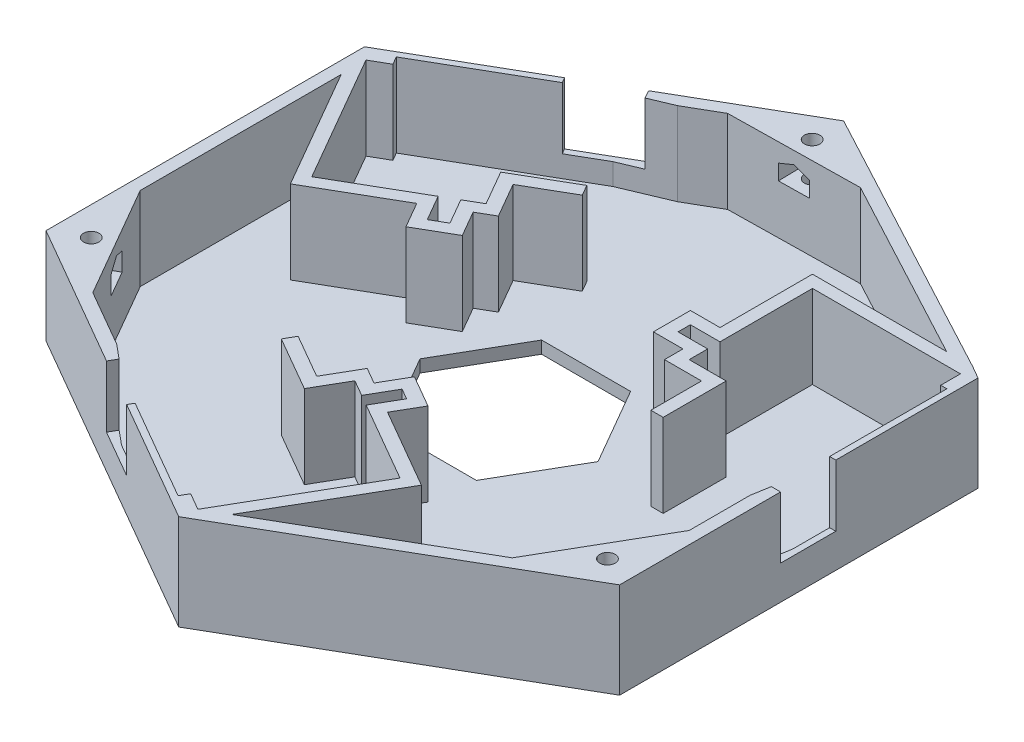
SolidWorks part; units mm, degrees
ref_plane "Front Plane" through (0, 0, 0) normal (0, 0, 1) x (1, 0, 0)
ref_plane "Top Plane" through (0, 0, 0) normal (0, 1, 0) x (1, 0, 0)
ref_plane "Right Plane" through (0, 0, 0) normal (1, 0, 0) x (0, 0, -1)
sketch "Sketch1" plane through (0, 0, 0) normal (0, 1, 0) x (1, 0, 0)
  line L1 (127, 0) -> (-63.5, 109.9852)
  line L2 (-63.5, 109.9852) -> (-63.5, -109.9852)
  line L3 (-63.5, -109.9852) -> (127, 0)
  circle A0 centre (0, 0) radius 63.5 construction
  dimension "D1" = 127
extrude "Boss-Extrude1" add sketch "Sketch1" along normal blind 15.5
sketch "Sketch2" plane through (0, 15.5, 0) normal (0, 1, 0) x (1, 0, 0)
  line L0 (-63.5, -109.9852) -> (16.5, -63.7972)
  line L1 (-63.5, -109.9852) -> (127, 0) construction
  line L2 (-63.5, 109.9852) -> (-63.5, -109.9852) construction
  line L3 (16.5, -63.7972) -> (-63.5, -17.6092)
  line L4 (-63.5, -17.6092) -> (-63.5, -109.9852)
  line L5 (-63.5, 109.9852) -> (16.5, 63.7972)
  line L6 (127, 0) -> (-63.5, 109.9852) construction
  line L7 (16.5, 63.7972) -> (-63.5, 17.6092)
  line L8 (-63.5, 17.6092) -> (-63.5, 109.9852)
  line L9 (127, 0) -> (47, 46.188)
  line L10 (47, 46.188) -> (47, -46.188)
  line L11 (47, -46.188) -> (127, 0)
  dimension "D1" = 80
  dimension "D2" = 110.5
extrude "Cut-Extrude1" cut sketch "Sketch2" against normal blind 24
sketch "Sketch3" plane through (0, 15.5, 0) normal (0, 1, 0) x (1, 0, 0)
  line L0 (47, 0) -> (-63.5, 0) construction
  line L1 (47, 46.188) -> (47, -46.188) construction
  line L2 (-63.5, 17.6092) -> (-63.5, -17.6092) construction
  line L3 (-23.5, 40.7032) -> (31.75, -54.9926) construction
  line L4 (-63.5, 17.6092) -> (16.5, 63.7972) construction
  line L5 (16.5, -63.7972) -> (47, -46.188) construction
  line L6 (-23.5, -40.7032) -> (31.75, 54.9926) construction
  line L7 (16.5, -63.7972) -> (-63.5, -17.6092) construction
  line L8 (47, 46.188) -> (16.5, 63.7972) construction
  line L14 (21, 28.2173) -> (21, 13.2173)
  line L15 (21, 13.2173) -> (16.2, 13.2173)
  line L25 (16.2, 13.2173) -> (16.2, 11.2173)
  line L26 (16.2, 11.2173) -> (21, 11.2173)
  line L27 (21, 11.2173) -> (21, 8.2173)
  line L28 (21, 8.2173) -> (27, 8.2173)
  line L38 (45, 28.2173) -> (21, 28.2173)
  line L41 (46, 21.2173) -> (46, 25.0173)
  line L42 (46, 25.0173) -> (45, 25.0173)
  line L43 (45, 25.0173) -> (45, 28.2173)
  line L84 (27, 8.2173) -> (27, 0)
  line L85 (27, 0) -> (45, 0)
  line L91 (14.1869, -31.8622) -> (1.1965, -24.3622)
  line L92 (1.1965, -24.3622) -> (3.5965, -20.2052)
  line L93 (3.5965, -20.2052) -> (1.8644, -19.2052)
  line L94 (1.8644, -19.2052) -> (-0.5356, -23.3622)
  line L95 (-0.5356, -23.3622) -> (-3.1336, -21.8622)
  line L96 (-3.1336, -21.8622) -> (-6.1336, -27.0583)
  line L97 (2.1869, -52.6468) -> (14.1869, -31.8622)
  line L99 (-4.6253, -50.4458) -> (-1.3344, -52.3458)
  line L100 (-1.3344, -52.3458) -> (-0.5844, -51.0468)
  line L101 (-0.5844, -51.0468) -> (2.1869, -52.6468)
  line L102 (-6.1336, -27.0583) -> (-13.25, -22.9497)
  line L103 (-13.25, -22.9497) -> (-22.25, -38.5381)
  line L105 (-35.285, 3.2995) -> (-22.2947, 10.7995)
  line L106 (-22.2947, 10.7995) -> (-19.8947, 6.6426)
  line L107 (-19.8947, 6.6426) -> (-17.5644, 7.988)
  line L108 (-17.5644, 7.988) -> (-19.9644, 12.1449)
  line L109 (-19.9644, 12.1449) -> (-17.3664, 13.6449)
  line L110 (-17.3664, 13.6449) -> (-20.6164, 19.2741)
  line L111 (-47.285, 24.0841) -> (-35.285, 3.2995)
  line L113 (-41.3747, 29.2285) -> (-45.2638, 26.9832)
  line L114 (-45.2638, 26.9832) -> (-44.5138, 25.6841)
  line L115 (-44.5138, 25.6841) -> (-47.285, 24.0841)
  line L116 (-20.6164, 19.2741) -> (-13.5, 23.3827)
  line L117 (-13.5, 23.3827) -> (-22.5, 38.9711)
  line L119 (-22.25, -38.5381) -> (-23, -39.8372)
  line L120 (-23, -39.8372) -> (-4.6253, -50.4458)
  line L121 (-41.3747, 29.2285) -> (-23, 39.8372)
  line L122 (-23, 39.8372) -> (-22.5, 38.9711)
  line L123 (45, 0) -> (46, 0)
  line L124 (46, 0) -> (46, 21.2173)
  dimension "D1" = 8.2173
  dimension "D2" = 3
  dimension "D3" = 4.8
  dimension "D4" = 6
  dimension "D5" = 2
  dimension "D6" = 15
  dimension "D7" = 24
  dimension "D8" = 1
  dimension "D9" = 3.8
  dimension "D12" = 1.5
  dimension "D13" = 1
  dimension "D14" = 24
  dimension "D15" = 18
  dimension "D16" = 18
  dimension "D17" = 6
  dimension "D18" = 4.8
  dimension "D19" = 1
  dimension "D21" = 8.2173
  dimension "D22" = 3.2
  dimension "D23" = 15
  dimension "D24" = 4.8
  dimension "D26" = 3
extrude "Cut-Extrude2" cut sketch "Sketch3" against normal blind 13.5
sketch "Sketch4" plane through (0, 15.5, 0) normal (0, 1, 0) x (1, 0, 0)
  line L0 (3.6689, -54.0798) -> (16.5, -61.4878)
  line L4 (25, -2) -> (25, 6.2173)
  line L5 (25, 6.2173) -> (19, 6.2173)
  line L6 (19, 6.2173) -> (19, 9.2173)
  line L7 (19, 9.2173) -> (14.2, 9.2173)
  line L8 (14.2, 9.2173) -> (14.2, 15.2173)
  line L9 (14.2, 15.2173) -> (19, 15.2173)
  line L10 (19, 15.2173) -> (19, 30.2173)
  line L11 (19, 30.2173) -> (45, 30.2173)
  line L12 (45, 30.2173) -> (45, 45.0333)
  line L13 (45, 45.0333) -> (26.5, 55.7143)
  line L14 (26.5, 55.7143) -> (6.5, 55.7143)
  line L17 (-10.7679, 22.6506) -> (-17.8843, 18.542)
  line L18 (-17.8843, 18.542) -> (-14.6343, 12.9128)
  line L19 (-14.6343, 12.9128) -> (-17.2324, 11.4128)
  line L20 (-17.2324, 11.4128) -> (-14.8324, 7.2559)
  line L21 (-14.8324, 7.2559) -> (-20.6267, 3.9106)
  line L22 (-20.6267, 3.9106) -> (-23.0267, 8.0675)
  line L23 (-23.0267, 8.0675) -> (-36.0171, 0.5675)
  line L24 (-36.0171, 0.5675) -> (-49.2671, 23.5172)
  line L25 (-49.2671, 23.5172) -> (-61.5, 16.4545)
  line L26 (-61.5, 16.4545) -> (-61.5, -4.9075)
  line L27 (-61.5, -4.9075) -> (-51.5, -22.228)
  line L30 (-13.9821, -20.2176) -> (-6.8657, -24.3263)
  line L31 (-6.8657, -24.3263) -> (-3.8657, -19.1301)
  line L32 (-3.8657, -19.1301) -> (-1.2676, -20.6301)
  line L33 (-1.2676, -20.6301) -> (1.1324, -16.4732)
  line L34 (1.1324, -16.4732) -> (6.3285, -19.4732)
  line L35 (6.3285, -19.4732) -> (3.9285, -23.6301)
  line L36 (3.9285, -23.6301) -> (16.9189, -31.1301)
  line L37 (16.9189, -31.1301) -> (3.6689, -54.0798)
  line L38 (16.5, -61.4878) -> (35, -50.8068)
  line L39 (35, -50.8068) -> (45, -33.4863)
  line L41 (-63.5, 17.6092) -> (-63.5, -17.6092) construction
  line L42 (16.5, -63.7972) -> (-63.5, -17.6092) construction
  line L43 (-17.5644, 7.988) -> (-19.9644, 12.1449) construction
  line L44 (-6.1336, -27.0583) -> (-13.25, -22.9497) construction
  line L45 (-3.1336, -21.8622) -> (-6.1336, -27.0583) construction
  line L46 (16.5, -63.7972) -> (47, -46.188) construction
  line L47 (2.1869, -52.6468) -> (14.1869, -31.8622) construction
  line L48 (14.1869, -31.8622) -> (1.1965, -24.3622) construction
  line L49 (1.8644, -19.2052) -> (-0.5356, -23.3622) construction
  line L50 (1.1965, -24.3622) -> (3.5965, -20.2052) construction
  line L51 (47, 46.188) -> (47, -46.188) construction
  line L52 (-47.285, 24.0841) -> (-35.285, 3.2995) construction
  line L53 (-63.5, 17.6092) -> (16.5, 63.7972) construction
  line L54 (47, 46.188) -> (16.5, 63.7972) construction
  line L55 (-35.285, 3.2995) -> (-22.2947, 10.7995) construction
  line L56 (-22.2947, 10.7995) -> (-19.8947, 6.6426) construction
  line L57 (-19.8947, 6.6426) -> (-17.5644, 7.988) construction
  line L58 (-19.9644, 12.1449) -> (-17.3664, 13.6449) construction
  line L59 (-17.3664, 13.6449) -> (-20.6164, 19.2741) construction
  line L60 (-20.6164, 19.2741) -> (-13.5, 23.3827) construction
  line L62 (14.1869, -31.8622) -> (1.1965, -24.3622) construction
  line L63 (3.5965, -20.2052) -> (1.8644, -19.2052) construction
  line L64 (-0.5356, -23.3622) -> (-3.1336, -21.8622) construction
  line L65 (-6.1336, -27.0583) -> (-13.25, -22.9497) construction
  line L67 (45, 28.2173) -> (21, 28.2173) construction
  line L69 (16.2, 11.2173) -> (21, 11.2173) construction
  line L70 (21, 13.2173) -> (16.2, 13.2173) construction
  line L71 (16.2, 13.2173) -> (16.2, 11.2173) construction
  line L72 (21, 28.2173) -> (21, 13.2173) construction
  line L73 (21, 8.2173) -> (27, 8.2173) construction
  line L74 (21, 11.2173) -> (21, 8.2173) construction
  line L75 (27, 8.2173) -> (27, 0) construction
  line L76 (-13.9821, -20.2176) -> (-23.7321, -37.1051)
  line L77 (-51.5, -22.228) -> (-27.6235, -36.0131)
  line L78 (-27.6235, -36.0131) -> (-23, -39.8372)
  line L79 (-23, -39.8372) -> (-22, -38.1051)
  line L80 (-13.25, -22.9497) -> (-23, -39.8372) construction
  line L81 (-22, -38.1051) -> (-23.7321, -37.1051)
  line L82 (6.5, 55.7143) -> (-15.6261, 42.9398)
  line L83 (-15.6261, 42.9398) -> (-23, 39.8372)
  line L84 (-23, 39.8372) -> (-22, 38.1051)
  line L85 (-13.5, 23.3827) -> (-23, 39.8372) construction
  line L86 (-22, 38.1051) -> (-20.2679, 39.1051)
  line L87 (-20.2679, 39.1051) -> (-10.7679, 22.6506)
  line L88 (45, -33.4863) -> (45, -5.9161)
  line L89 (45, -5.9161) -> (46, 0)
  line L90 (46, 0) -> (44, 0)
  line L91 (27, 0) -> (46, 0) construction
  line L92 (44, 0) -> (44, -2)
  line L93 (44, -2) -> (25, -2)
  point P75 (-15.9333, 12.1628)
  point P88 (-1.8346, -22.6122)
  point P89 (-4.6336, -24.4602)
  point P98 (31.75, -54.9926)
  dimension "D2" = 2
  dimension "D4" = 2
  dimension "D5" = 2
  dimension "D6" = 2
  dimension "D7" = 2
  dimension "D8" = 2
  dimension "D9" = 2
  dimension "D10" = 2
  dimension "D11" = 2
  dimension "D12" = 2
  dimension "D13" = 2
  dimension "D14" = 2
  dimension "D15" = 2
  dimension "D16" = 2
  dimension "D17" = 2
  dimension "D18" = 2
  dimension "D19" = 2
  dimension "D20" = 2
  dimension "D21" = 2
  dimension "D22" = 2
  dimension "D23" = 2
  dimension "D24" = 2
  dimension "D25" = 2
  dimension "D26" = 6
  dimension "D27" = 2
  dimension "D28" = 2
  dimension "D29" = 2
  dimension "D30" = 2
  dimension "D31" = 2
  dimension "D32" = 2
  dimension "D33" = 2
  dimension "D34" = 2
  dimension "D35" = 2
  dimension "D36" = 20
  dimension "D37" = 20
  dimension "D38" = 20
  dimension "D39" = 2
  dimension "D40" = 6
  dimension "D41" = 2
  dimension "D42" = 8
  dimension "D43" = 2
  dimension "D44" = 2
  dimension "D45" = 2
  dimension "D46" = 2
  dimension "D47" = 2
extrude "Cut-Extrude3" cut sketch "Sketch4" against normal blind 13.5
sketch "Sketch5" plane through (0, 2, 0) normal (0, 1, 0) x (1, 0, 0)
  line L1 (14.4338, 0) -> (7.2169, 12.5)
  line L2 (7.2169, 12.5) -> (-7.2169, 12.5)
  line L3 (-7.2169, 12.5) -> (-14.4338, 0)
  line L4 (-14.4338, 0) -> (-7.2169, -12.5)
  line L5 (-7.2169, -12.5) -> (7.2169, -12.5)
  line L6 (7.2169, -12.5) -> (14.4338, 0)
  circle A0 centre (0, 0) radius 12.5 construction
  dimension "D1" = 25
extrude "Cut-Extrude4" cut sketch "Sketch5" against normal blind 13.5
sketch "Sketch6" plane through (0, 15.5, 0) normal (0, 1, 0) x (1, 0, 0)
  line L6 (41.75, -43.1569) -> (43.5, -44.1673) construction
  line L7 (-58.25, -14.5781) -> (-60, -15.5885) construction
  line L8 (16.5, 57.735) -> (16.5, 59.7558) construction
  circle A3 centre (-59.125, -15.0833) radius 1.15
  circle A4 centre (16.5, 58.7454) radius 1.15
  circle A5 centre (42.625, -43.6621) radius 1.15
  dimension "D1" = 2.3
  dimension "D2" = 2.3
  dimension "D3" = 2.3
extrude "Cut-Extrude5" cut sketch "Sketch6" against normal blind 10.5
sketch "Sketch8" plane through (-48.25, 0, 27.8572) normal (0.866, 0, -0.5) x (-0.5, 0, -0.866)
  line L0 (16.5, 15.5) -> (16.5, 5.1)
  line L3 (26.5, 15.5) -> (6.5, 15.5) construction
  line L9 (14, 6.1) -> (19, 6.1)
  line L10 (14, 6.1) -> (14, 4.1)
  line L11 (14, 4.1) -> (19, 4.1)
  line L12 (19, 6.1) -> (19, 4.1)
  line L13 (14, 6.1) -> (19, 4.1) construction
  line L14 (14, 4.1) -> (19, 6.1) construction
  point P6 (16.5, 9.7316)
  dimension "D1" = 2
  dimension "D2" = 5
  dimension "D3" = 10.4
extrude "Cut-Extrude7" cut sketch "Sketch8" against normal blind 5.5 contours L9 L12 L11 L10
sketch "Sketch9" plane through (48.25, 0, 27.8572) normal (-0.866, 0, -0.5) x (-0.5, 0, 0.866)
  line L0 (16.5, 15.5) -> (16.5, 5.1) construction
  line L1 (26.5, 15.5) -> (6.5, 15.5) construction
  line L3 (14, 6.1) -> (19, 6.1)
  line L4 (14, 6.1) -> (14, 4.1)
  line L5 (14, 4.1) -> (19, 4.1)
  line L6 (19, 6.1) -> (19, 4.1)
  line L7 (14, 6.1) -> (19, 4.1) construction
  line L8 (14, 4.1) -> (19, 6.1) construction
  dimension "D1" = 2
  dimension "D2" = 5
extrude "Cut-Extrude8" cut sketch "Sketch9" against normal blind 5.5
sketch "Sketch10" plane through (0, 0, -55.7143) normal (0, 0, 1) x (1, 0, 0)
  line L0 (16.5, 15.5) -> (16.5, 5.1) construction
  line L1 (26.5, 15.5) -> (6.5, 15.5) construction
  line L3 (14, 6.1) -> (19, 6.1)
  line L4 (14, 6.1) -> (14, 4.1)
  line L5 (14, 4.1) -> (19, 4.1)
  line L6 (19, 6.1) -> (19, 4.1)
  line L7 (14, 6.1) -> (19, 4.1) construction
  line L8 (14, 4.1) -> (19, 6.1) construction
  dimension "D1" = 2
  dimension "D2" = 5
extrude "Cut-Extrude9" cut sketch "Sketch10" against normal blind 5.5
sketch "Sketch12" plane through (0, 15.5, 0) normal (0, 1, 0) x (1, 0, 0)
  line L0 (-49.2671, 23.5172) -> (-49.2671, -25.8266)
  line L1 (16.5, -63.7972) -> (-63.5, -17.6092) construction
  line L2 (-49.2671, -25.8266) -> (-63.5, -17.6092)
  line L3 (-63.5, -17.6092) -> (-63.5, 17.6092)
  line L4 (-63.5, 17.6092) -> (-49.2671, 25.8266)
  line L5 (-63.5, 17.6092) -> (16.5, 63.7972) construction
  line L6 (-49.2671, 25.8266) -> (-49.2671, 23.5172)
  line L7 (3.6689, -54.0798) -> (47, -29.0626)
  line L8 (47, 46.188) -> (47, -46.188) construction
  line L9 (47, -29.0626) -> (47, -46.188)
  line L10 (47, -46.188) -> (16.5, -63.7972)
  line L11 (16.5, -63.7972) -> (1.6689, -55.2345)
  line L12 (3.6689, -54.0798) -> (1.6689, -55.2345)
  line L13 (45, 30.2173) -> (0, 54.2709)
  line L14 (0, 54.2709) -> (16.5, 63.7972)
  line L15 (16.5, 63.7972) -> (47, 46.188)
  line L16 (47, 46.188) -> (16.5, 63.7972) construction
  line L17 (45, 30.2173) -> (47, 29.0626)
  line L18 (47, 29.0626) -> (47, 46.188)
extrude "Cut-Extrude10" cut sketch "Sketch12" against normal blind 20
sketch "Sketch13" plane through (0, 2, 0) normal (0, 1, 0) x (1, 0, 0)
  line L0 (-49.2671, -23.5172) -> (-49.2671, 23.5172)
  line L1 (-36.0171, 0.5675) -> (-49.2671, 23.5172) construction
  line L2 (-36.0171, 0.5675) -> (-49.2671, 23.5172) construction
  line L3 (-49.2671, 23.5172) -> (-47.2671, 20.0531)
  line L4 (-47.2671, 20.0531) -> (-47.2671, -24.6719)
  line L5 (-49.2671, -23.5172) -> (-27.6235, -36.0131) construction
  line L6 (-47.2671, -24.6719) -> (-49.2671, -23.5172)
  line L7 (45, -30.2173) -> (3.6689, -54.0798)
  line L8 (3.6689, -54.0798) -> (5.6689, -50.6157)
  line L9 (16.9189, -31.1301) -> (3.6689, -54.0798) construction
  line L10 (5.6689, -50.6157) -> (45, -27.9079)
  line L11 (45, -30.2173) -> (45, -5.9161) construction
  line L12 (45, -27.9079) -> (45, -30.2173)
  line L13 (45, 30.2173) -> (2.077, 53.1607)
  line L14 (0.0374, 51.9831) -> (40.7574, 30.2173)
  line L15 (2.077, 53.1607) -> (0.0374, 51.9831)
  line L16 (2.077, 53.1607) -> (-15.6261, 42.9398) construction
  line L17 (19, 30.2173) -> (45, 30.2173) construction
  line L18 (40.7574, 30.2173) -> (45, 30.2173)
  dimension "D1" = 2
  dimension "D2" = 2
  dimension "D3" = 2
extrude "Boss-Extrude2" add sketch "Sketch13" along normal blind 13.5
sketch "Sketch14" plane through (0, 2, 0) normal (0, 1, 0) x (1, 0, 0)
  line L0 (-47.2671, -24.6719) -> (-36.7671, -30.734)
  line L1 (-47.2671, -24.6719) -> (-27.6235, -36.0131) construction
  line L2 (-36.7671, -30.734) -> (-47.2671, -12.5475)
  line L3 (-47.2671, -24.6719) -> (-47.2671, 20.0531) construction
  line L4 (-47.2671, -12.5475) -> (-47.2671, -24.6719)
  line L5 (0.0374, 51.9831) -> (-10.4626, 45.921)
  line L6 (0.0374, 51.9831) -> (-15.6261, 42.9398) construction
  line L7 (-10.4626, 45.921) -> (10.7301, 46.2676)
  line L8 (0.0374, 51.9831) -> (40.7574, 30.2173) construction
  line L9 (10.7301, 46.2676) -> (0.0374, 51.9831)
  line L10 (45, -27.9079) -> (45, -15.7835)
  line L11 (45, -27.9079) -> (45, -5.9161) construction
  line L12 (45, -15.7835) -> (34.5, -33.97)
  line L13 (45, -27.9079) -> (5.6689, -50.6157) construction
  line L14 (34.5, -33.97) -> (45, -27.9079)
  dimension "D1" = 21
  dimension "D2" = 6.0622
  dimension "D3" = 21.1927
  dimension "D4" = 21
extrude "Boss-Extrude3" add sketch "Sketch14" along normal blind 13.5
sketch "Sketch15" plane through (0, 15.5, 0) normal (0, 1, 0) x (1, 0, 0)
  line L0 (-44.6152, -23.1408) -> (-42.0171, -21.6408) construction
  line L3 (0.0669, 49.0943) -> (0.1338, 46.0943) construction
  line L5 (42.3481, -26.3768) -> (39.75, -24.8768) construction
  line L7 (-36.7671, -30.734) -> (-47.2671, -12.5475) construction
  line L8 (-10.4626, 45.921) -> (10.7301, 46.2676) construction
  line L9 (45, -15.7835) -> (34.5, -33.97) construction
  circle A0 centre (-44.6152, -23.1408) radius 1.25
  circle A1 centre (42.3481, -26.3768) radius 1.25
  circle A2 centre (0.0669, 49.0943) radius 1.25
  dimension "D1" = 2.5
  dimension "D2" = 3
  dimension "D3" = 3
  dimension "D4" = 3
extrude "Cut-Extrude11" cut sketch "Sketch15" against normal blind 8.5
sketch "Sketch16" plane through (-0.7538, 0, -46.0798) normal (0.0164, 0, 0.9999) x (0.9999, 0, -0.0164)
  line L0 (0.8877, 15.5) -> (0.8877, 7) construction
  line L1 (0.8877, 12.5) -> (0.8877, 13.5) construction
  line L2 (-1.6123, 12.5) -> (0.8877, 13.5)
  line L3 (-9.7101, 15.5) -> (11.4854, 15.5) construction
  line L4 (0.8877, 13.5) -> (3.3877, 12.5)
  line L6 (-1.6123, 12.5) -> (-1.6123, 10)
  line L7 (-1.6123, 10) -> (3.3877, 10)
  line L8 (3.3877, 12.5) -> (3.3877, 10)
  line L9 (-1.6123, 12.5) -> (3.3877, 10) construction
  line L10 (-1.6123, 10) -> (3.3877, 12.5) construction
  point P4 (0.8877, 11.25)
  dimension "D1" = 2.5
  dimension "D2" = 5
sketch "Sketch17" plane through (-40.8835, 0, 23.6041) normal (0.866, 0, -0.5) x (-0.5, 0, -0.866)
  line L0 (2.2671, 15.5) -> (2.2671, 7) construction
  line L1 (-8.2329, 15.5) -> (12.7671, 15.5) construction
  line L2 (2.2671, 12.5) -> (2.2671, 13.5) construction
  line L4 (-0.2329, 12.5) -> (-0.2329, 9.5)
  line L5 (-0.2329, 9.5) -> (4.7671, 9.5)
  line L6 (4.7671, 12.5) -> (4.7671, 9.5)
  line L7 (-0.2329, 12.5) -> (4.7671, 9.5) construction
  line L8 (-0.2329, 9.5) -> (4.7671, 12.5) construction
  line L9 (-0.2329, 12.5) -> (2.2671, 13.5)
  line L10 (2.2671, 13.5) -> (4.7671, 12.5)
  point P4 (2.2671, 11)
  dimension "D1" = 5
  dimension "D2" = 3
sketch "Sketch18" plane through (40.5845, 0, 23.4314) normal (-0.866, 0, -0.5) x (-0.5, 0, 0.866)
  line L0 (1.6689, 15.5) -> (1.6689, 7) construction
  line L1 (-8.8311, 15.5) -> (12.1689, 15.5) construction
  line L2 (1.6689, 12.5) -> (1.6689, 13.5) construction
  line L4 (-0.8311, 12.5) -> (-0.8311, 9.5)
  line L5 (-0.8311, 9.5) -> (4.1689, 9.5)
  line L6 (4.1689, 12.5) -> (4.1689, 9.5)
  line L7 (-0.8311, 12.5) -> (4.1689, 9.5) construction
  line L8 (-0.8311, 9.5) -> (4.1689, 12.5) construction
  line L9 (-0.8311, 12.5) -> (1.6689, 13.5)
  line L10 (1.6689, 13.5) -> (4.1689, 12.5)
  point P4 (1.6689, 11)
  dimension "D1" = 5
  dimension "D2" = 3
sketch "Sketch19" plane through (0, 15.5, 0) normal (0, 1, 0) x (1, 0, 0)
  line L0 (-13.25, -22.9497) -> (-22, -38.1051)
  line L1 (-22, -38.1051) -> (-23.7321, -37.1051)
  line L2 (-23.7321, -37.1051) -> (-14.9821, -21.9497)
  line L3 (-23.7321, -37.1051) -> (-13.9821, -20.2176) construction
  line L4 (-14.9821, -21.9497) -> (-13.25, -22.9497)
  line L5 (-13.5, 23.3827) -> (-22, 38.1051)
  line L6 (-22, 38.1051) -> (-20.2679, 39.1051)
  line L7 (-20.2679, 39.1051) -> (-11.7679, 24.3827)
  line L8 (-20.2679, 39.1051) -> (-10.7679, 22.6506) construction
  line L9 (-11.7679, 24.3827) -> (-13.5, 23.3827)
  line L11 (27, 0) -> (44, 0)
  line L12 (27, 0) -> (27, -2)
  line L13 (27, -2) -> (44, -2)
  line L14 (44, 0) -> (44, -2)
extrude "Cut-Extrude15" cut sketch "Sketch19" against normal blind 13.5
sketch "Sketch20" plane through (0, 15.5, 0) normal (0, 1, 0) x (1, 0, 0)
  line L2 (46, 0) -> (45.5, -2.958)
  line L4 (45, -5.9161) -> (46, 0) construction
  line L7 (-23, 39.8372) -> (-28.1962, 36.8372)
  line L9 (-41.3747, 29.2285) -> (-23, 39.8372) construction
  line L14 (-28.1962, 36.8372) -> (-28.6962, 37.7032)
  line L16 (-49.2671, 25.8266) -> (0, 54.2709) construction
  line L18 (46, 0) -> (46, 6)
  line L19 (46, 0) -> (46, 21.2173) construction
  line L20 (46, 6) -> (47, 6)
  line L21 (47, 29.0626) -> (47, -29.0626) construction
  line L22 (47, 6) -> (47, 0)
  line L23 (-23, -39.8372) -> (-17.8038, -42.8372)
  line L24 (-23, -39.8372) -> (-4.6253, -50.4458) construction
  line L25 (-17.8038, -42.8372) -> (-18.3038, -43.7032)
  line L26 (1.6689, -55.2345) -> (-49.2671, -25.8266) construction
  line L27 (-18.3038, -43.7032) -> (-23.5, -40.7032)
  line L28 (-28.6962, 37.7032) -> (-23.5, 40.7032)
  line L29 (45.5, -2.958) -> (47, -2.958)
  line L30 (47, -2.958) -> (47, 0)
  line L31 (-23, -39.8372) -> (-25.3117, -37.9251)
  line L32 (-27.6235, -36.0131) -> (-23, -39.8372) construction
  line L33 (-25.3117, -37.9251) -> (-26.0617, -39.2242)
  line L34 (-26.0617, -39.2242) -> (-23.5, -40.7032)
  line L35 (-23, 39.8372) -> (-19.3131, 41.3885)
  line L36 (-15.6261, 42.9398) -> (-23, 39.8372) construction
  line L37 (-19.3131, 41.3885) -> (-20.0631, 42.6875)
  line L38 (-20.0631, 42.6875) -> (-23.5, 40.7032)
  dimension "D1" = 6
  dimension "D2" = 6
  dimension "D3" = 6
extrude "Cut-Extrude16" cut sketch "Sketch20" against normal blind 10
extrude "Cut-Extrude17" cut sketch "Sketch16" against normal blind 5.7
extrude "Cut-Extrude18" cut sketch "Sketch17" against normal blind 5.7
extrude "Cut-Extrude19" cut sketch "Sketch18" against normal blind 5.7
